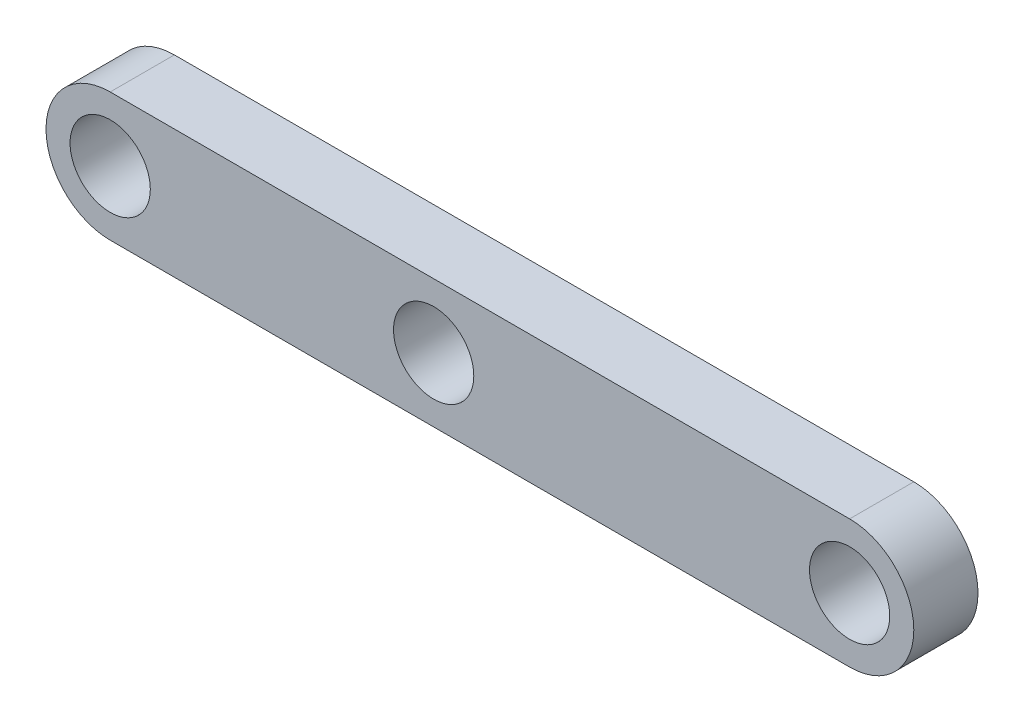
SolidWorks part; units mm, degrees
ref_plane "Front Plane" through (0, 0, 0) normal (0, 0, 1) x (1, 0, 0)
ref_plane "Top Plane" through (0, 0, 0) normal (0, 1, 0) x (1, 0, 0)
ref_plane "Right Plane" through (0, 0, 0) normal (1, 0, 0) x (0, 0, -1)
sketch "Sketch1" plane through (0, 0, 0) normal (0, 0, 1) x (1, 0, 0)
  line L1 (-8, -3.175) -> (28.575, -3.175)
  line L3 (-8, 3.175) -> (28.575, 3.175)
  circle A0 centre (8, 0) radius 1.9844
  circle A1 centre (-8, 0) radius 1.9844
  circle A2 centre (28.575, 0) radius 1.9844
  arc A3 (-8, 3.175) -> (-8, -3.175) centre (-8, 0) ccw
  arc A4 (28.575, -3.175) -> (28.575, 3.175) centre (28.575, 0) ccw
  dimension "D1" = 8
  dimension "D2" = 28.575
  dimension "D5" = 3.9688
  dimension "D6" = 3.9688
  dimension "D7" = 3.9688
  dimension "D3" = 3.175
  dimension "D4" = 3.175
extrude "Boss-Extrude1" add sketch "Sketch1" along normal blind 3.175
